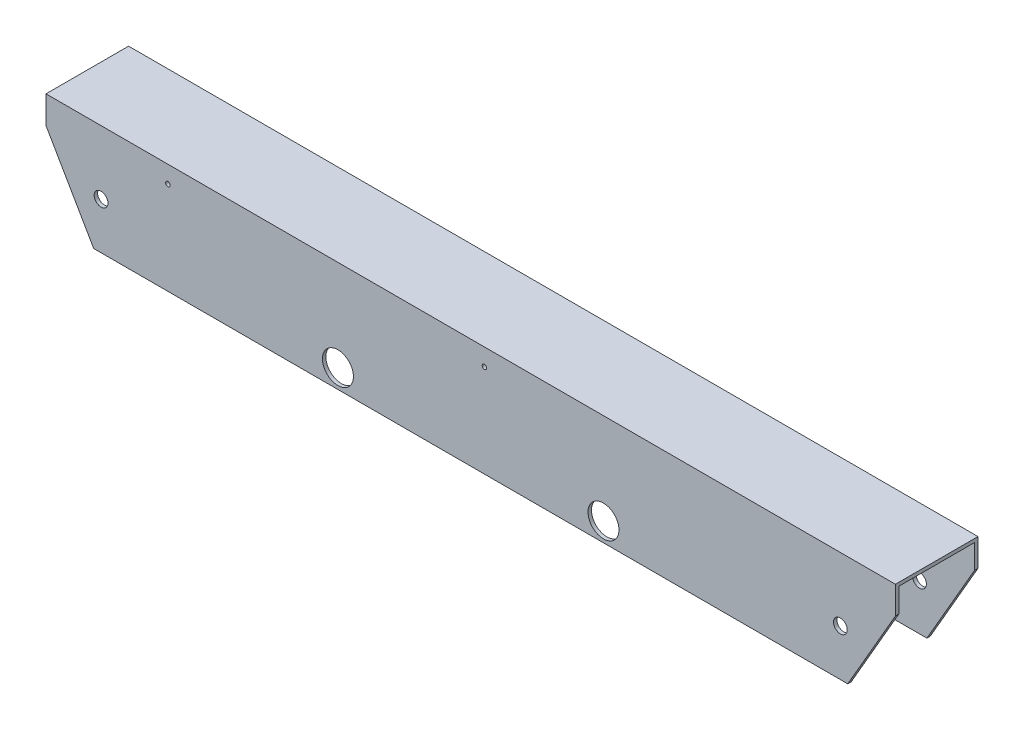
SolidWorks part; units mm, degrees
ref_plane "Front Plane" through (0, 0, 0) normal (0, 0, 1) x (1, 0, 0)
ref_plane "Top Plane" through (0, 0, 0) normal (0, 1, 0) x (1, 0, 0)
ref_plane "Right Plane" through (0, 0, 0) normal (1, 0, 0) x (0, 0, -1)
sketch "Sketch1" plane through (0, 0, 0) normal (1, 0, 0) x (0, 0, -1)
  line L0 (-34.925, 47.625) -> (-34.925, -47.625) construction
  line L1 (-38.1, 50.8) -> (38.1, 50.8)
  line L2 (-38.1, 50.8) -> (-38.1, -50.8)
  line L3 (-38.1, -50.8) -> (-34.925, -50.8)
  line L4 (38.1, 50.8) -> (38.1, -50.8)
  line L5 (-38.1, 50.8) -> (38.1, -50.8) construction
  line L6 (-38.1, -50.8) -> (38.1, 50.8) construction
  line L7 (34.925, 47.625) -> (34.925, -50.8)
  line L8 (-34.925, 47.625) -> (34.925, 47.625)
  line L9 (-34.925, 47.625) -> (-34.925, -50.8)
  line L10 (-34.925, -47.625) -> (34.925, -47.625) construction
  line L11 (34.925, 47.625) -> (34.925, -47.625) construction
  line L12 (-38.1, -50.8) -> (38.1, -50.8) construction
  line L13 (38.1, -50.8) -> (34.925, -50.8)
  point P0 (0, 0)
  dimension "D1" = 76.2
  dimension "D2" = 101.6
  dimension "D3" = 3.175
extrude "Boss-Extrude1" add sketch "Sketch1" along normal mid plane 783.7315
sketch "Sketch2" plane through (0, 0, 38.1) normal (0, 0, 1) x (1, 0, 0)
  line L1 (-391.8658, 50.8) -> (-391.8658, -50.8) construction
  line L8 (391.8658, -50.8) -> (-391.8658, -50.8) construction
  line L9 (0, -55) -> (0, 55) construction
  line L13 (0, 50.8) -> (0, -55.872) construction
  line L14 (391.8658, 50.8) -> (-391.8658, 50.8) construction
  circle A0 centre (-341.0658, -7.9375) radius 6.35
  circle A1 centre (122.5118, -33.3375) radius 14.2875
  circle A2 centre (341.0658, -7.9375) radius 6.35
  circle A4 centre (12.7, 34.925) radius 2.0828
  circle A5 centre (-279.4, 34.925) radius 2.0828
  circle A6 centre (-122.5118, -33.3375) radius 14.2875
  dimension "D1" = 122.5118
  dimension "D2" = 17.4625
  dimension "D3" = 220.025
  dimension "D4" = 218.5539
  dimension "D5" = 28.575
  dimension "D6" = 25.4
  dimension "D7" = 12.7
  dimension "D8" = 50.8
  dimension "D9" = 28.575
  dimension "D10" = 12.7
  dimension "D11" = 220.025
  dimension "D12" = 25.4
  dimension "D13" = 17.4625
  dimension "D22" = 15.875
  dimension "D23" = 15.875
  dimension "D24" = 112.4658
extrude "Cut-Extrude1" cut sketch "Sketch2" against normal blind 141.732
sketch "Sketch13" [suppressed] plane through (0, 0, 38.1) normal (0, 0, -1) x (-1, 0, 0)
  line L0 (-391.8658, -50.8) -> (391.8658, -50.8) construction
  line L2 (-25.4, 22.225) -> (0, 22.225)
  line L3 (-25.4, 22.225) -> (-25.4, 47.625)
  line L4 (-25.4, 47.625) -> (0, 47.625)
  line L5 (0, 22.225) -> (0, 47.625)
  line L6 (-25.4, 22.225) -> (0, 47.625) construction
  line L7 (-25.4, 47.625) -> (0, 22.225) construction
  line L8 (266.7, 22.225) -> (292.1, 22.225)
  line L9 (266.7, 22.225) -> (266.7, 47.625)
  line L10 (266.7, 47.625) -> (292.1, 47.625)
  line L11 (292.1, 22.225) -> (292.1, 47.625)
  line L12 (266.7, 22.225) -> (292.1, 47.625) construction
  line L13 (266.7, 47.625) -> (292.1, 22.225) construction
  circle A0 centre (-160.6118, -35.1235) radius 3.302
  circle A1 centre (-122.5118, -33.3375) radius 14.2875 construction
  circle A2 centre (-160.6118, 41.0765) radius 3.302
  circle A3 centre (-84.4118, 41.0765) radius 3.302
  circle A4 centre (-84.4118, -35.1235) radius 3.302
  point P12 (-12.7, 34.925)
  point P18 (279.4, 34.925)
  dimension "D1" = 6.604
  dimension "D2" = 15.6765
  dimension "D3" = 38.1
  dimension "D4" = 76.2
  dimension "D5" = 76.2
  dimension "D6" = 76.2
  dimension "D7" = 38.1
  dimension "D8" = 15.6765
  dimension "D9" = 25.4
  dimension "D10" = 25.4
  dimension "D11" = 25.4
  dimension "D12" = 25.4
extrude "Cut-Extrude11" [suppressed] cut sketch "Sketch13" along normal blind 33.2436
sketch "Sketch14" plane through (0, 0, -38.1) normal (0, 0, -1) x (-1, 0, 0)
  line L0 (-391.8658, -50.8) -> (391.8658, -50.8) construction
  line L2 (-25.4, 22.225) -> (0, 22.225)
  line L3 (-25.4, 22.225) -> (-25.4, 47.625)
  line L4 (-25.4, 47.625) -> (0, 47.625)
  line L5 (0, 22.225) -> (0, 47.625)
  line L6 (-25.4, 22.225) -> (0, 47.625) construction
  line L7 (-25.4, 47.625) -> (0, 22.225) construction
  line L8 (266.7, 22.225) -> (292.1, 22.225)
  line L9 (266.7, 22.225) -> (266.7, 47.625)
  line L10 (266.7, 47.625) -> (292.1, 47.625)
  line L11 (292.1, 22.225) -> (292.1, 47.625)
  line L12 (266.7, 22.225) -> (292.1, 47.625) construction
  line L13 (266.7, 47.625) -> (292.1, 22.225) construction
  circle A0 centre (-160.6118, -35.1235) radius 3.302
  circle A1 centre (-160.6118, 41.0765) radius 3.302
  circle A2 centre (-84.4118, 41.0765) radius 3.302
  circle A3 centre (-84.4118, -35.1235) radius 3.302
  circle A4 centre (-122.5118, -33.3375) radius 14.2875 construction
  point P12 (-12.7, 34.925)
  point P18 (279.4, 34.925)
  dimension "D1" = 6.604
  dimension "D2" = 15.6765
  dimension "D3" = 76.2
  dimension "D4" = 76.2
  dimension "D5" = 76.2
  dimension "D6" = 38.1
  dimension "D7" = 25.4
  dimension "D8" = 25.4
  dimension "D9" = 25.4
  dimension "D10" = 25.4
extrude "Cut-Extrude12" cut sketch "Sketch14" against normal blind 23.114
sketch "Sketch16" plane through (0, 0, 38.1) normal (0, 0, 1) x (1, 0, 0)
  line L1 (-391.8658, 50.8) -> (-391.8658, -50.8) construction
  line L2 (-391.8658, 25.4) -> (-347.8717, -50.8)
  line L3 (391.8658, -50.8) -> (-391.8658, -50.8) construction
  line L4 (-347.8717, -50.8) -> (-391.8658, -50.8)
  line L5 (-391.8658, -50.8) -> (-391.8658, 25.4)
  line L6 (0, 50.8) -> (0, -65.171) construction
  line L7 (0, -55) -> (0, 55) construction
  line L9 (347.8717, -50.8) -> (391.8658, -50.8)
  line L10 (391.8658, -50.8) -> (391.8658, 25.4)
  line L11 (391.8658, 25.4) -> (347.8717, -50.8)
  dimension "D1" = 60
  dimension "D2" = 76.2
  dimension "D4" = 43.9941
extrude "Cut-Extrude13" cut sketch "Sketch16" against normal blind 101.6
